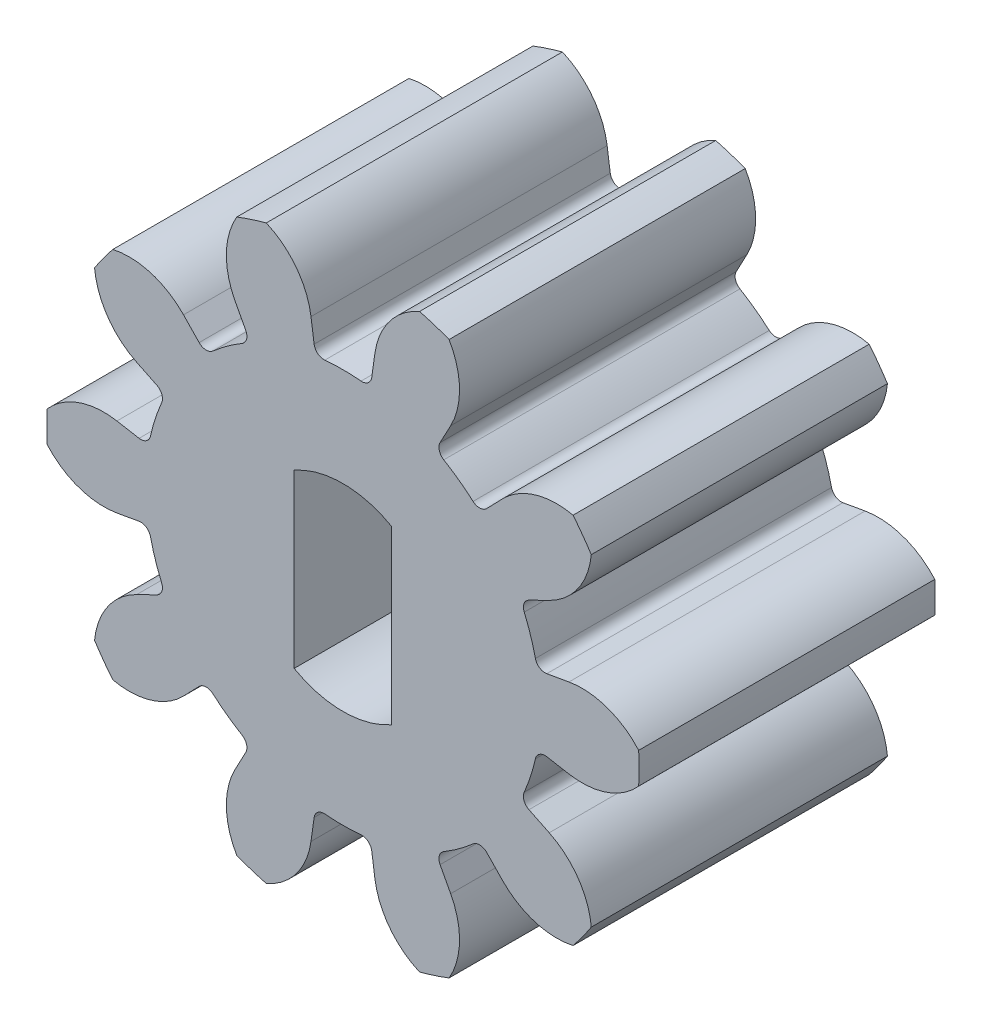
SolidWorks part; units mm, degrees
ref_plane "Front Plane" through (0, 0, 0) normal (0, 0, 1) x (1, 0, 0)
ref_plane "Top Plane" through (0, 0, 0) normal (0, 1, 0) x (1, 0, 0)
ref_plane "Right Plane" through (0, 0, 0) normal (1, 0, 0) x (0, 0, -1)
sketch "Sketch1" plane through (0, 0, 0) normal (0, 0, 1) x (1, 0, 0)
  line L0 (0, 0) -> (9.7603, 0) construction
  line L1 (0, 0) -> (9.1385, 2.9693) construction
  line L2 (0, 0) -> (9.3575, 1.65) construction
  line L3 (0, 0) -> (7.8775, 0.4128) construction
  line L4 (4.5794, 0.8075) -> (3.9376, 0.6943)
  line L5 (0, 0) -> (3.8027, 1.2356)
  line L6 (4.5794, -0.8075) -> (3.9376, -0.6943)
  line L7 (0, 0) -> (3.8027, -1.2356)
  circle A0 centre (0, 0) radius 6 construction
  circle A1 centre (0, 0) radius 4.65 construction
  circle A2 centre (0, 0) radius 4 construction
  arc A3 (4.5794, 0.8075) -> (5.9918, 0.314) centre (4.8451, -0.6999) cw
  arc A4 (3.8027, 1.2356) -> (3.9376, 0.6943) centre (0, 0) cw
  arc A5 (5.9918, 0.314) -> (5.9918, -0.314) centre (0, 0) cw
  arc A6 (4.5794, -0.8075) -> (5.9918, -0.314) centre (4.8451, 0.6999) ccw
  arc A7 (3.8027, -1.2356) -> (3.9376, -0.6943) centre (0, 0) ccw
  dimension "D1" = 12
  dimension "D2" = 8
  dimension "D3" = 9.3
  dimension "D4" = 18
  dimension "D5" = 10
  dimension "D6" = 3
extrude "Boss-Extrude1" add sketch "Sketch1" along normal blind 6 contours L7 A7 L6 A6 A5 A3 L4 A4 L5
fillet "Fillet3" radius 0.2 1 edges at (3.9376, 0.6943, 3)
fillet "Fillet4" radius 0.2 1 edges at (3.9376, -0.6943, 3)
pattern_circular "CirPattern1" count 10 over 360 about axis through (0, 0, 0) along (0, 0, 1) of "Boss-Extrude1", "Fillet3", "Fillet4"
sketch "Sketch2" plane through (0, 0, 0) normal (0, 0, 1) x (1, 0, 0)
  line L2 (-0.9886, 1.739) -> (-0.9886, -1.739)
  line L4 (0.9886, 1.739) -> (0.9886, -1.739)
  line L5 (0, -1.739) -> (0, 1.739) construction
  line L6 (-0.9886, 0) -> (0.9886, 0) construction
  arc A0 (-0.9886, 1.739) -> (0.9886, 1.739) centre (0, 0) cw
  arc A1 (-0.9886, -1.739) -> (0.9886, -1.739) centre (0, 0) ccw
extrude "Cut-Extrude1" cut sketch "Sketch2" against normal blind 6 and the other way through all
